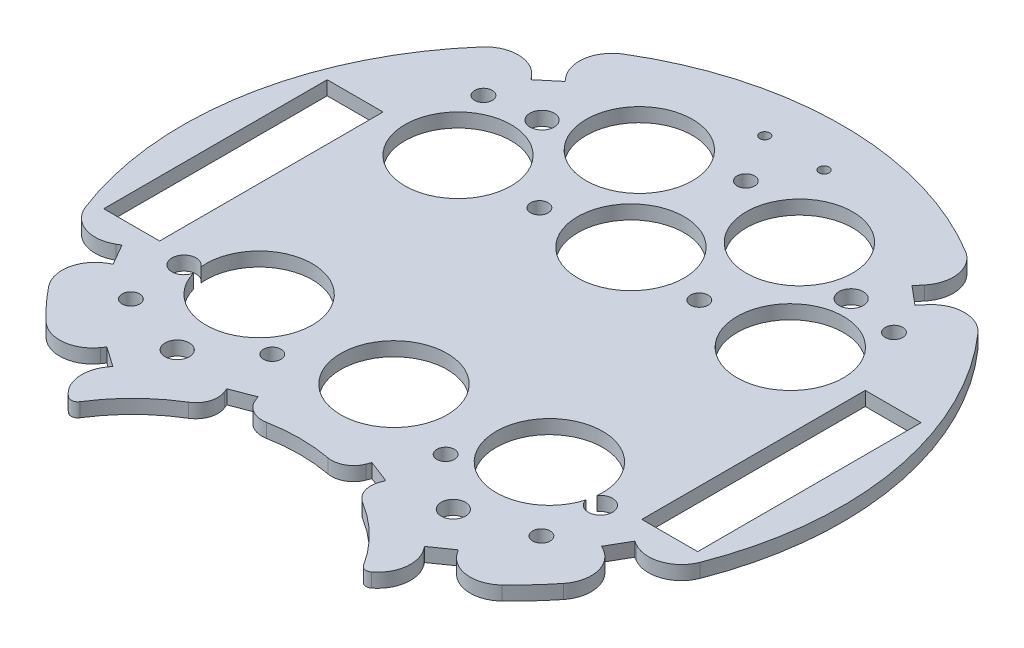
SolidWorks part; units mm, degrees
ref_plane "Front Plane" through (0, 0, 0) normal (0, 0, 1) x (1, 0, 0)
ref_plane "Top Plane" through (0, 0, 0) normal (0, 1, 0) x (1, 0, 0)
ref_plane "Right Plane" through (0, 0, 0) normal (1, 0, 0) x (0, 0, -1)
sketch "Sketch1" plane through (0, 0, 0) normal (0, 1, 0) x (1, 0, 0)
  line L0 (0, 0) -> (-32.9956, -67.352) construction
  line L1 (0, 86.2583) -> (0, -96.8543) construction
  line L2 (0, 0) -> (32.9956, -67.352) construction
  line L3 (-32.9956, -67.352) -> (0, -86.402) construction
  line L4 (32.9956, -67.352) -> (0, -86.402) construction
  line L5 (0, 0) -> (-13.6167, -50.8184) construction
  line L6 (0, 0) -> (-43.0182, -61.4364) construction
  line L7 (0, 0) -> (-48.2091, 57.4533) construction
  line L8 (-83.3992, 0) -> (107.0959, 0) construction
  line L9 (54.8141, -25.4) -> (54.8141, 25.4)
  line L10 (-67.5141, -25.4) -> (-54.8141, -25.4)
  line L11 (-67.5141, -25.4) -> (-67.5141, 25.4)
  line L12 (-67.5141, 25.4) -> (-54.8141, 25.4)
  line L13 (-54.8141, 25.4) -> (-54.8141, -25.4)
  line L14 (67.5141, 25.4) -> (54.8141, 25.4)
  line L15 (67.5141, -25.4) -> (67.5141, 25.4)
  line L16 (67.5141, -25.4) -> (54.8141, -25.4)
  line L17 (0, 0) -> (13.6167, -50.8184) construction
  line L18 (-64.9519, -37.5) -> (0, 0) construction
  line L19 (0, 0) -> (48.2091, 57.4533) construction
  line L20 (0, 0) -> (43.0182, -61.4364) construction
  line L21 (64.9519, -37.5) -> (0, 0) construction
  line L22 (-36.0148, -56.2289) -> (-35.4412, -55.4097)
  line L23 (12.5843, -45.8219) -> (12.9417, -44.8879)
  line L24 (0, 92.0255) -> (0, -91.0871) construction
  line L25 (-17.721, -47.7876) -> (-18.0784, -46.8536)
  line L26 (36.0148, -56.2289) -> (35.4412, -55.4097)
  line L27 (-59.1537, -30.9773) -> (-58.2877, -30.4773)
  line L28 (59.1537, -30.9773) -> (58.2877, -30.4773)
  line L29 (40.7784, 52.876) -> (39.4928, 51.3439)
  line L30 (-44.668, -58.998) -> (-44.6824, -59.0187)
  line L31 (-58.2877, -30.4773) -> (-55.5379, -35.24)
  line L32 (-35.4412, -55.4097) -> (-39.9465, -52.2551)
  line L33 (-40.7784, 52.876) -> (-40.1356, 52.11)
  line L34 (-55.5379, -35.24) -> (-56.404, -35.74)
  line L35 (-39.9465, -52.2551) -> (-40.5201, -53.0742)
  line L36 (-18.0784, -46.8536) -> (-12.9417, -44.8879)
  line L37 (-12.9417, -44.8879) -> (-12.5843, -45.8219)
  line L38 (12.9417, -44.8879) -> (18.0784, -46.8536)
  line L39 (18.0784, -46.8536) -> (17.721, -47.7876)
  line L40 (35.4412, -55.4097) -> (39.9465, -52.2551)
  line L41 (39.9465, -52.2551) -> (40.5201, -53.0742)
  line L42 (-13.6167, -50.8184) -> (-2.8571, -46.701) construction
  line L43 (58.2877, -30.4773) -> (55.5379, -35.24)
  line L44 (55.5379, -35.24) -> (56.404, -35.74)
  line L45 (-13.6167, -50.8184) -> (-17.7255, -40.0812) construction
  line L46 (39.4928, 51.3439) -> (43.706, 47.8086)
  line L47 (43.706, 47.8086) -> (44.9916, 49.3407)
  line L48 (-40.1356, 52.11) -> (-44.3488, 48.5746)
  line L49 (-44.3488, 48.5746) -> (-44.9916, 49.3407)
  line L50 (-95.2583, 0) -> (95.2368, 0) construction
  arc A0 (-56.3744, 49.4664) -> (-69.893, -27.2023) centre (0, 0) ccw
  arc A1 (-19.7932, -53.8469) -> (-32.2407, -66.1006) centre (0, -86.402) ccw
  arc A2 (38.9256, 64.1077) -> (-38.9256, 64.1077) centre (0, 0) ccw
  arc A3 (56.3744, 49.4664) -> (44.9916, 49.3407) centre (50.737, 44.5198) ccw
  arc A4 (-56.3744, 49.4664) -> (-44.9916, 49.3407) centre (-50.737, 44.5198) cw
  arc A5 (-69.893, -27.2023) -> (-59.1537, -30.9773) centre (-62.9037, -24.4821) ccw
  arc A6 (-51.8486, -54.1915) -> (-40.5201, -53.0742) centre (-46.6637, -48.7724) ccw
  arc A7 (-38.9256, 64.1077) -> (-40.7784, 52.876) centre (-35.033, 57.6969) ccw
  arc A8 (-58.5044, -46.928) -> (-56.404, -35.74) centre (-52.654, -42.2352) cw
  arc A9 (-34.4197, -66.4939) -> (-36.0148, -56.2289) centre (-29.8711, -60.5307) cw
  arc A10 (38.9256, 64.1077) -> (40.7784, 52.876) centre (35.033, 57.6969) cw
  arc A11 (58.5044, -46.928) -> (56.404, -35.74) centre (52.654, -42.2352) ccw
  arc A12 (69.893, -27.2023) -> (59.1537, -30.9773) centre (62.9037, -24.4821) cw
  arc A13 (34.4197, -66.4939) -> (36.0148, -56.2289) centre (29.8711, -60.5307) ccw
  arc A14 (51.8486, -54.1915) -> (40.5201, -53.0742) centre (46.6637, -48.7724) cw
  arc A15 (-58.5044, -46.928) -> (-51.8486, -54.1915) centre (0, 0) ccw
  arc A16 (-33.1901, -67.2563) -> (-32.9956, -67.352) centre (0, 0) ccw
  arc A17 (51.8486, -54.1915) -> (58.5044, -46.928) centre (0, 0) ccw
  arc A18 (69.893, -27.2023) -> (56.3744, 49.4664) centre (0, 0) ccw
  arc A19 (-19.7932, -53.8469) -> (-17.721, -47.7876) centre (-22.3908, -49.5745) ccw
  arc A20 (-6.9964, -48.9499) -> (-12.5843, -45.8219) centre (-7.9145, -44.0349) cw
  arc A21 (19.7932, -53.8469) -> (17.721, -47.7876) centre (22.3908, -49.5745) cw
  arc A22 (6.9964, -48.9499) -> (12.5843, -45.8219) centre (7.9145, -44.0349) ccw
  arc A23 (6.9964, -48.9499) -> (-6.9964, -48.9499) centre (0, -86.402) ccw
  arc A24 (32.2407, -66.1006) -> (19.7932, -53.8469) centre (0, -86.402) ccw
  circle A25 centre (-18.179, 24.3106) radius 2
  circle A26 centre (-32.9956, -24.5929) radius 12.095
  circle A27 centre (32.9956, -24.5929) radius 12.095
  circle A28 centre (37.7724, 25.4) radius 12.095
  circle A29 centre (-37.7724, 25.4) radius 12.075
  circle A30 centre (-18.1963, 47.0458) radius 12.095
  circle A31 centre (18.1963, 47.0458) radius 12.095
  circle A32 centre (0, 26.9383) radius 12.095
  circle A33 centre (0, -26.9383) radius 12.095
  circle A38 centre (-46.6637, -40.0812) radius 2
  circle A39 centre (46.6637, -40.0812) radius 2
  circle A40 centre (46.6637, 40.0812) radius 2
  circle A41 centre (-46.6637, 40.0812) radius 2
  arc A42 (-34.4197, -66.4939) -> (-32.2407, -66.1006) centre (-33.51, -65.3013) ccw
  arc A43 (34.4197, -66.4939) -> (32.2407, -66.1006) centre (33.51, -65.3013) cw
  circle A44 centre (-6.731, 64.1077) radius 1.143
  circle A45 centre (6.731, 64.1077) radius 1.143
  circle A46 centre (-31.3845, -44.8217) radius 2.75
  circle A47 centre (18.179, 24.3106) radius 2
  circle A48 centre (0, 53.0612) radius 2
  circle A49 centre (-47.3324, -27.3273) radius 2.75
  circle A50 centre (-35.1341, 41.8711) radius 2.75
  circle A51 centre (-19.7094, -34.8968) radius 2
  circle A52 centre (35.1341, 41.8711) radius 2.75
  circle A53 centre (47.3324, -27.3273) radius 2.75
  circle A54 centre (31.3845, -44.8217) radius 2.75
  circle A55 centre (19.7094, -34.8968) radius 2
  point P14 (-62.6039, 0)
  point P23 (62.6039, 0)
  point P35 (-31.3845, -44.8217)
  point P40 (-46.7211, -26.9744)
  point P45 (-34.6777, 41.3272)
  point P122 (-29.8711, 0)
  dimension "D1" = 150
  dimension "D3" = 120
  dimension "D2" = 76.2
  dimension "D11" = 1
  dimension "D15" = 13.462
  dimension "D18" = 2.286
  dimension "D12" = 4
  dimension "D4" = 25.4
  dimension "D5" = 12.7
  dimension "D6" = 80
  dimension "D7" = 80
  dimension "D8" = 25
  dimension "D9" = 30
  dimension "D14" = 75.5448
  dimension "D16" = 36.3925
  dimension "D19" = 65.9911
  dimension "D21" = 24.5929
extrude "Boss-Extrude1" add sketch "Sketch1" along normal blind 3.175
